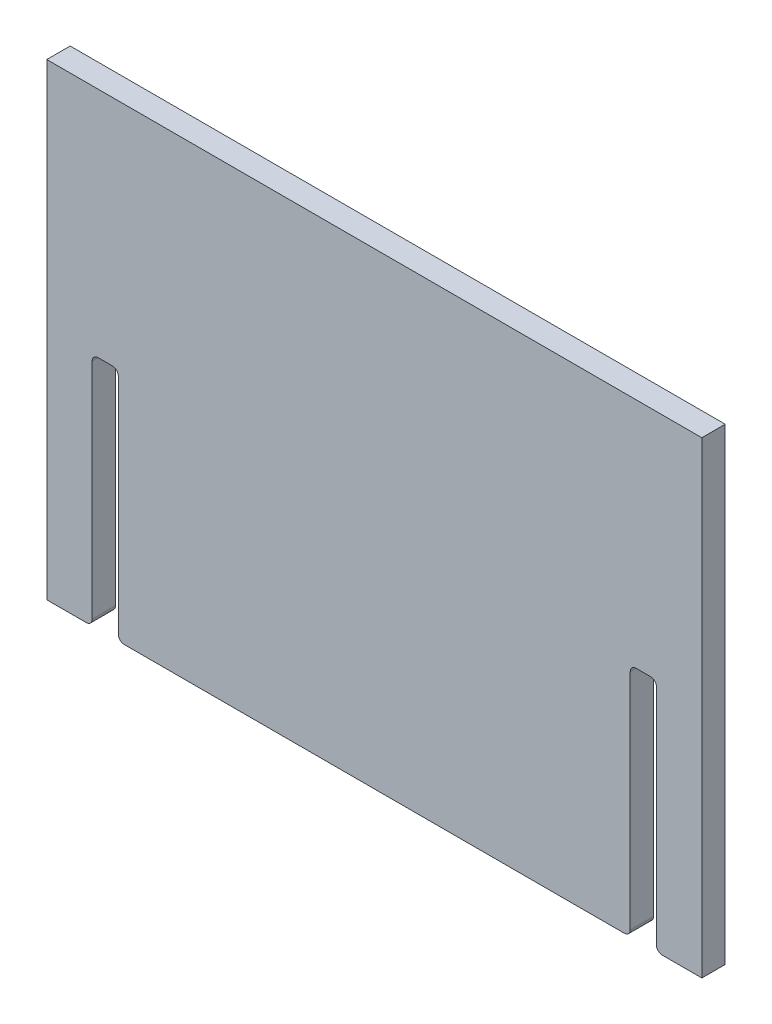
SolidWorks part; units mm, degrees
ref_plane "Front Plane" through (0, 0, 0) normal (0, 0, 1) x (1, 0, 0)
ref_plane "Top Plane" through (0, 0, 0) normal (0, 1, 0) x (1, 0, 0)
ref_plane "Right Plane" through (0, 0, 0) normal (1, 0, 0) x (0, 0, -1)
sketch "Sketch1" plane through (0, 0, 0) normal (0, 0, 1) x (1, 0, 0)
  line L7 (1294.204, -519.4799) -> (1294.204, -532.1799) construction
  line L8 (1294.204, -24.1799) -> (1649.804, -24.1799)
  line L9 (1294.204, -24.1799) -> (1294.204, -278.1799)
  line L11 (1649.804, -24.1799) -> (1649.804, -278.1799)
  line L12 (1649.804, -519.4799) -> (1649.804, -532.1799) construction
  line L13 (1332.304, -24.1799) -> (1319.604, -24.1799) construction
  line L14 (1294.204, -278.1799) -> (1319.604, -278.1799)
  line L15 (1319.604, -24.1799) -> (1319.604, -519.4799) construction
  line L16 (1319.604, -278.1799) -> (1319.604, -151.1799)
  line L17 (1319.604, -151.1799) -> (1332.304, -151.1799)
  line L18 (1332.304, -24.1799) -> (1332.304, -519.4799) construction
  line L19 (1332.304, -151.1799) -> (1332.304, -278.1799)
  line L20 (1332.304, -278.1799) -> (1611.704, -278.1799)
  line L21 (1611.704, -24.1799) -> (1611.704, -519.4799) construction
  line L22 (1611.704, -278.1799) -> (1611.704, -151.1799)
  line L23 (1611.704, -151.1799) -> (1624.404, -151.1799)
  line L24 (1624.404, -24.1799) -> (1624.404, -519.4799) construction
  line L25 (1624.404, -151.1799) -> (1624.404, -278.1799)
  line L26 (1624.404, -278.1799) -> (1649.804, -278.1799)
  dimension "D1" = 127
  dimension "D2" = 254
extrude "Boss-Extrude1" add sketch "Sketch1" along normal mid plane 12.7
other "Move Face slot" face at (1611.704, -214.6799, 0) face at (1624.404, -214.6799, 0) face at (1618.054, -151.1799, 0) face at (1332.304, -214.6799, 0) face at (1325.954, -151.1799, 0) face at (1319.604, -214.6799, 0) parameters "D1"=0.762
fillet "Fillet1" radius 3.175 8 edges at (1610.942, -278.1799, 0) (1625.166, -278.1799, 0) (1333.066, -278.1799, 0) (1318.842, -278.1799, 0) (1625.166, -150.4179, 0) (1610.942, -150.4179, 0) (1333.066, -150.4179, 0) (1318.842, -150.4179, 0)
